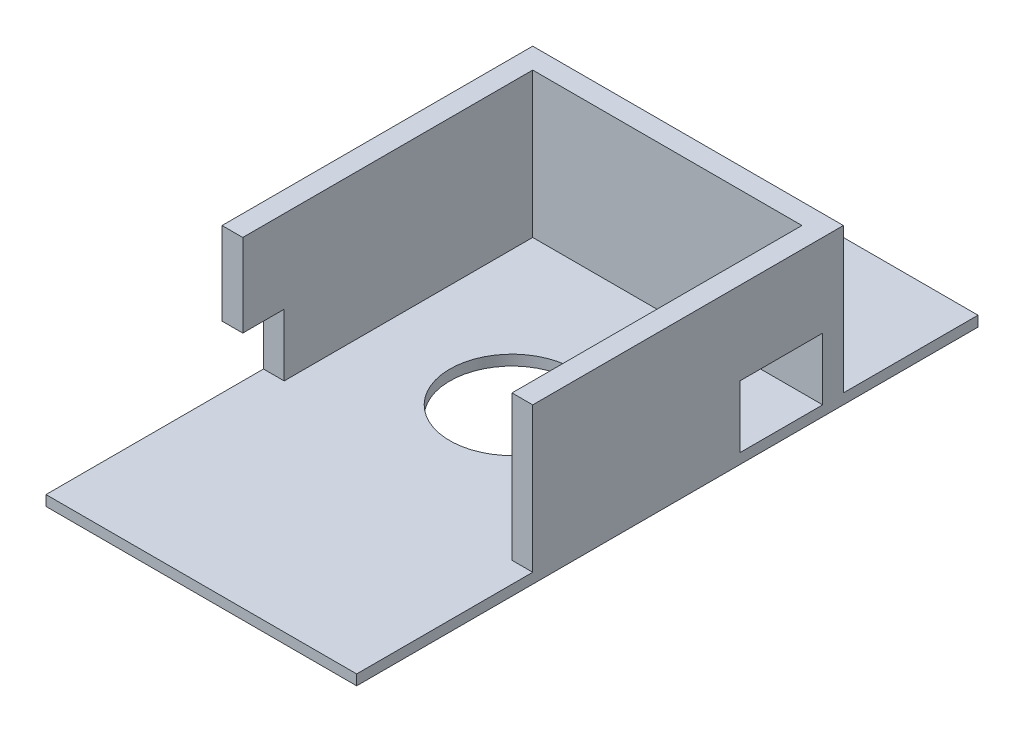
SolidWorks part; units mm, degrees
ref_plane "Front Plane" through (0, 0, 0) normal (0, 0, 1) x (1, 0, 0)
ref_plane "Top Plane" through (0, 0, 0) normal (0, 1, 0) x (1, 0, 0)
ref_plane "Right Plane" through (0, 0, 0) normal (1, 0, 0) x (0, 0, -1)
sketch "Sketch3" plane through (0, 0, 0) normal (0, 1, 0) x (1, 0, 0)
  line L1 (-33.1781, 22.4899) -> (41.8219, 22.4899)
  line L2 (-33.1781, 22.4899) -> (-33.1781, -62.5101)
  line L3 (-33.1781, -62.5101) -> (41.8219, -62.5101)
  line L4 (41.8219, 22.4899) -> (41.8219, -62.5101)
  dimension "D1" = 85
  dimension "D2" = 75
extrude "Boss-Extrude1" add sketch "Sketch3" along normal blind 35
sketch "Sketch4" plane through (0, 35, 0) normal (0, 1, 0) x (1, 0, 0)
  line L0 (41.8219, 22.4899) -> (-33.1781, 22.4899) construction
  line L1 (-28.1781, 17.4899) -> (36.8219, 17.4899)
  line L2 (-28.1781, 17.4899) -> (-28.1781, -57.5101)
  line L3 (-28.1781, -57.5101) -> (36.8219, -57.5101)
  line L4 (36.8219, 17.4899) -> (36.8219, -57.5101)
  line L5 (41.8219, -62.5101) -> (41.8219, 22.4899) construction
  line L6 (-33.1781, -62.5101) -> (41.8219, -62.5101) construction
  line L7 (-33.1781, 22.4899) -> (-33.1781, -62.5101) construction
  dimension "D1" = 5
  dimension "D2" = 5
  dimension "D3" = 5
  dimension "D4" = 5
extrude "Cut-Extrude1" cut sketch "Sketch4" against normal blind 40
sketch "Sketch8" plane through (0, 0, 0) normal (0, -1, 0) x (1, 0, 0)
  line L0 (41.8219, 62.5101) -> (41.8219, -22.4899) construction
  line L1 (-33.1781, 95.0101) -> (41.8219, 95.0101)
  line L2 (-33.1781, 95.0101) -> (-33.1781, -54.9899)
  line L3 (-33.1781, -54.9899) -> (41.8219, -54.9899)
  line L4 (41.8219, 95.0101) -> (41.8219, -54.9899)
  line L5 (-33.1781, -22.4899) -> (-33.1781, 62.5101) construction
  point P6 (41.8219, 20.0101)
  dimension "D1" = 150
  dimension "D2" = 75
  dimension "D3" = 0
  dimension "D4" = 0
extrude "Boss-Extrude2" add sketch "Sketch8" along normal blind 2.5
sketch "Sketch9" plane through (0, -2.5, 0) normal (0, -1, 0) x (1, 0, 0)
  line L0 (-33.1781, -54.9899) -> (41.8219, -54.9899) construction
  circle A0 centre (4.3219, 20.0101) radius 15
  dimension "D1" = 30
  dimension "D2" = 75
extrude "Cut-Extrude4" cut sketch "Sketch9" against normal blind 15
sketch "Sketch10" plane through (0, 0, 62.5101) normal (0, 0, 1) x (1, 0, 0)
  line L0 (41.8219, 35) -> (41.8219, 0) construction
  line L1 (-33.1781, 35) -> (41.8219, 35)
  line L2 (-33.1781, 35) -> (-33.1781, 1.9833)
  line L3 (-33.1781, 1.9833) -> (41.8219, 1.9833)
  line L4 (41.8219, 35) -> (41.8219, 1.9833)
extrude "Cut-Extrude5" cut sketch "Sketch10" against normal blind 10
sketch "Sketch16" plane through (-33.1781, 0, 0) normal (-1, 0, 0) x (0, 0, 1)
  line L0 (-22.4899, 35) -> (52.5101, 35) construction
  line L1 (62.5101, 0) -> (42.5101, 0)
  line L2 (62.5101, 0) -> (62.5101, 15)
  line L3 (62.5101, 15) -> (42.5101, 15)
  line L4 (42.5101, 0) -> (42.5101, 15)
  dimension "D1" = 20
  dimension "D2" = 20
extrude "Cut-Extrude6" cut sketch "Sketch16" against normal blind 10
sketch "Sketch17" plane through (-23.1781, 0, 0) normal (-1, 0, 0) x (0, 0, 1)
  line L1 (52.5101, 1.9833) -> (62.5101, 1.9833)
  line L2 (52.5101, 1.9833) -> (52.5101, 0)
  line L3 (52.5101, 0) -> (62.5101, 0)
  line L4 (62.5101, 1.9833) -> (62.5101, 0)
extrude "Cut-Extrude7" cut sketch "Sketch17" against normal through all
sketch "Sketch19" plane through (41.8219, 0, 0) normal (1, 0, 0) x (0, 0, -1)
  line L0 (22.4899, 35) -> (22.4899, 0) construction
  line L1 (-2.5101, 15) -> (17.4899, 15)
  line L2 (-2.5101, 15) -> (-2.5101, 0)
  line L3 (-2.5101, 0) -> (17.4899, 0)
  line L4 (17.4899, 15) -> (17.4899, 0)
  line L5 (54.9899, -2.5) -> (-95.0101, -2.5) construction
  line L9 (-52.5101, 35) -> (22.4899, 35) construction
  dimension "D1" = 5
  dimension "D2" = 20
  dimension "D3" = 2.5
  dimension "D4" = 20
extrude "Cut-Extrude8" cut sketch "Sketch19" against normal blind 10
